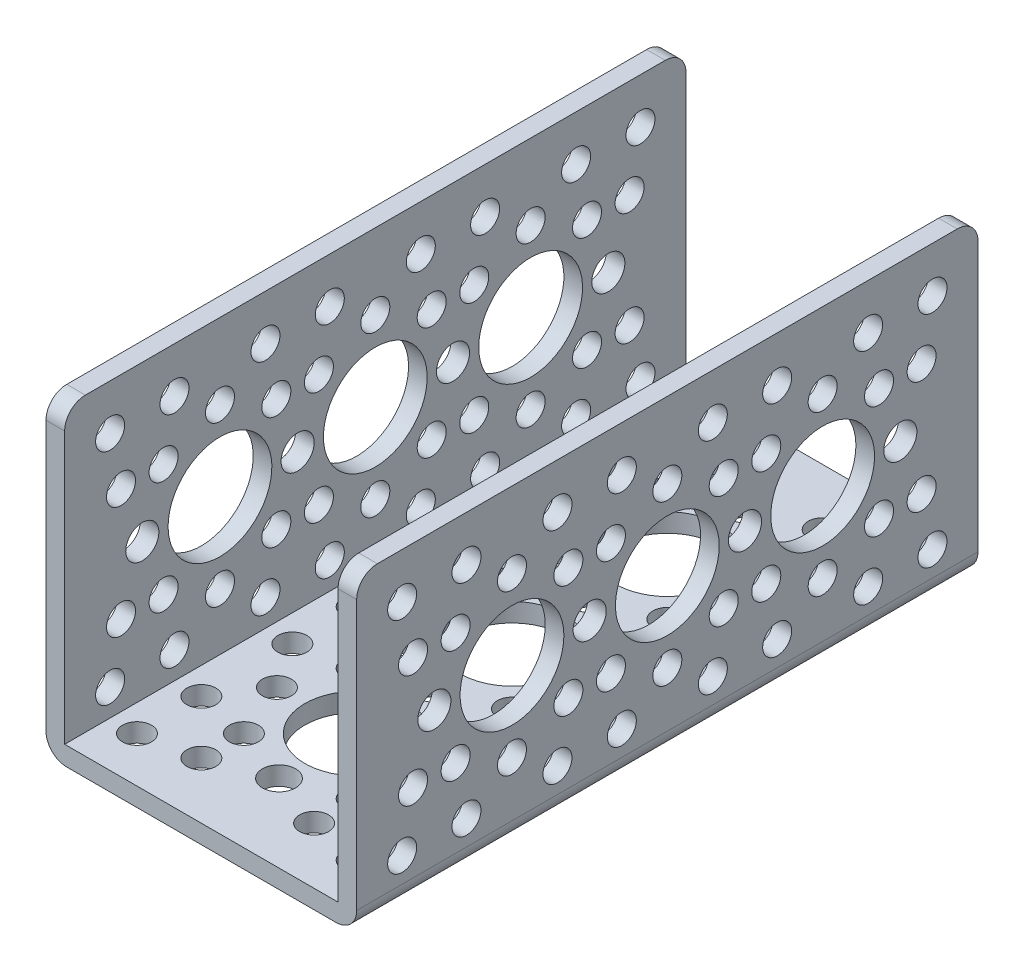
SolidWorks part; units mm, degrees
ref_plane "Front Plane" through (0, 0, 0) normal (0, 0, 1) x (1, 0, 0)
ref_plane "Top Plane" through (0, 0, 0) normal (0, 1, 0) x (1, 0, 0)
ref_plane "Right Plane" through (0, 0, 0) normal (1, 0, 0) x (0, 0, -1)
ref_plane "Plane1" through (0, 0, 0) normal (0, -1, 0) x (1, 0, 0)
sketch "Sketch1" plane through (0, 0, 0) normal (0, -1, 0) x (1, 0, 0)
  line L0 (38.1, 76.2) -> (0, 76.2)
  line L1 (0, 76.2) -> (0, 0)
  line L2 (0, 0) -> (38.1, 0)
  line L3 (38.1, 0) -> (38.1, 76.2)
extrude "Boss-Extrude1" add sketch "Sketch1" against normal blind 38.1
sketch "Sketch2" plane through (0, 0, 76.2) normal (0, 0, 1) x (1, 0, 0)
  line L0 (35.814, 38.1) -> (2.286, 38.1)
  line L1 (2.286, 38.1) -> (2.286, 2.286)
  line L2 (2.286, 2.286) -> (35.814, 2.286)
  line L3 (35.814, 2.286) -> (35.814, 38.1)
extrude "Cut-Extrude1" cut sketch "Sketch2" against normal through all
hole_wizard "Hole1" positions "Sketch4" profile "Sketch3" legacy
sketch "Sketch4" plane through (38.1, 0, 0) normal (1, 0, 0) x (0, 0, -1)
  point P0 (-38.1, 19.05)
  point P1 (-19.05, 19.05)
  point P2 (-57.15, 19.05)
sketch "Sketch3" plane through (38.1, 19.05, 38.1) normal (0, 1, 0) x (0, 0, -1)
  line L0 (0, 0) -> (0, 2.286)
  line L1 (0, 2.286) -> (6.3627, 2.286)
  line L2 (6.3627, 2.286) -> (6.3627, 0)
  line L3 (6.3627, 0) -> (0, 0)
  line L4 (0, 110) -> (0, -10) construction
  dimension "Diameter" = 12.7254
  dimension "Depth" = 2.286
hole_wizard "M3 Clearance Hole1" positions "Sketch6" profile "Sketch5" hole size "M3" standard "ANSI Metric"
sketch "Sketch6" plane through (38.1, 0, 0) normal (1, 0, 0) x (0, 0, -1)
  point P0 (-62.7296, 5.5796)
  point P1 (-69.2852, 12.1352)
  point P2 (-62.7296, 32.5204)
  point P3 (-69.2852, 25.9648)
  point P4 (-13.4704, 5.5796)
  point P5 (-6.9148, 12.1352)
  point P6 (-13.4704, 32.5204)
  point P7 (-6.9148, 25.9648)
  point P8 (-43.6796, 5.5796)
  point P9 (-24.6296, 5.5796)
  point P10 (-43.6796, 32.5204)
  point P11 (-24.6296, 32.5204)
  point P12 (-70.6204, 5.5796)
  point P13 (-70.6204, 32.5204)
  point P14 (-51.5704, 5.5796)
  point P15 (-51.5704, 32.5204)
  point P16 (-50.2352, 12.1352)
  point P17 (-57.15, 9.271)
  point P18 (-64.0648, 12.1352)
  point P19 (-64.0648, 25.9648)
  point P20 (-57.15, 28.829)
  point P21 (-31.1852, 12.1352)
  point P22 (-38.1, 9.271)
  point P23 (-45.0148, 12.1352)
  point P24 (-45.0148, 25.9648)
  point P25 (-38.1, 28.829)
  point P26 (-50.2352, 25.9648)
  point P27 (-31.1852, 25.9648)
  point P28 (-32.5204, 5.5796)
  point P29 (-32.5204, 32.5204)
  point P30 (-5.5796, 5.5796)
  point P31 (-5.5796, 32.5204)
  point P32 (-12.1352, 12.1352)
  point P33 (-19.05, 9.271)
  point P34 (-25.9648, 12.1352)
  point P35 (-25.9648, 25.9648)
  point P36 (-19.05, 28.829)
  point P37 (-12.1352, 25.9648)
sketch "Sketch5" plane through (38.1, 5.5796, 62.7296) normal (0, 1, 0) x (0, 0, -1)
  line L0 (0, 0) -> (0, 2.286)
  line L1 (0, 2.286) -> (1.778, 2.286)
  line L2 (1.778, 2.286) -> (1.778, 0)
  line L5 (1.778, 0) -> (0, 0)
  line L11 (0, -6.35) -> (0, 107.95) construction
  dimension "Thru Hole Dia." = 3.556
  dimension "Thru Hole Depth" = 2.286
hole_wizard "M3.5 Clearance Hole1" positions "Sketch8" profile "Sketch7" hole size "M3.5" standard "ANSI Metric"
sketch "Sketch8" plane through (38.1, 0, 0) normal (1, 0, 0) x (0, 0, -1)
  point P0 (-66.675, 19.05)
  point P1 (-47.625, 19.05)
  point P2 (-28.575, 19.05)
  point P3 (-9.525, 19.05)
sketch "Sketch7" plane through (38.1, 19.05, 66.675) normal (0, 1, 0) x (0, 0, -1)
  line L0 (0, 0) -> (0, 2.286)
  line L1 (0, 2.286) -> (2.032, 2.286)
  line L2 (2.032, 2.286) -> (2.032, 0)
  line L5 (2.032, 0) -> (0, 0)
  line L11 (0, -6.35) -> (0, 107.95) construction
  dimension "Thru Hole Dia." = 4.064
  dimension "Thru Hole Depth" = 2.286
hole_wizard "Hole2" positions "Sketch10" profile "Sketch9" legacy
sketch "Sketch10" plane through (0, 0, 0) normal (0, -1, 0) x (-1, 0, 0)
  point P0 (-19.05, -57.15)
  point P1 (-19.05, -38.1)
  point P2 (-19.05, -19.05)
sketch "Sketch9" plane through (19.05, 0, 57.15) normal (1, 0, 0) x (0, 0, -1)
  line L0 (0, 0) -> (0, 38.1)
  line L1 (0, 38.1) -> (6.3627, 38.1)
  line L2 (6.3627, 38.1) -> (6.3627, 0)
  line L3 (6.3627, 0) -> (0, 0)
  line L4 (0, 110) -> (0, -10) construction
  dimension "Diameter" = 12.7254
  dimension "Depth" = 38.1
hole_wizard "M3.5 Clearance Hole2" positions "Sketch12" profile "Sketch11" hole size "M3.5" standard "ANSI Metric"
sketch "Sketch12" plane through (0, 0, 0) normal (0, -1, 0) x (-1, 0, 0)
  point P0 (-19.05, -66.675)
  point P1 (-19.05, -47.625)
  point P2 (-19.05, -28.575)
  point P3 (-19.05, -9.525)
sketch "Sketch11" plane through (19.05, 0, 66.675) normal (1, 0, 0) x (0, 0, -1)
  line L0 (0, 0) -> (0, 38.1)
  line L1 (0, 38.1) -> (2.032, 38.1)
  line L2 (2.032, 38.1) -> (2.032, 0)
  line L5 (2.032, 0) -> (0, 0)
  line L11 (0, -6.35) -> (0, 107.95) construction
  dimension "Thru Hole Dia." = 4.064
  dimension "Thru Hole Depth" = 38.1
hole_wizard "M3 Clearance Hole2" positions "Sketch14" profile "Sketch13" hole size "M3" standard "ANSI Metric"
sketch "Sketch14" plane through (0, 0, 0) normal (0, -1, 0) x (-1, 0, 0)
  point P0 (-5.5796, -70.6204)
  point P1 (-5.5796, -62.7296)
  point P2 (-12.1352, -69.2852)
  point P3 (-32.5204, -70.6204)
  point P4 (-32.5204, -62.7296)
  point P5 (-25.9648, -69.2852)
  point P6 (-5.5796, -51.5704)
  point P7 (-5.5796, -43.6796)
  point P8 (-32.5204, -51.5704)
  point P9 (-32.5204, -43.6796)
  point P10 (-12.1352, -50.2352)
  point P11 (-9.271, -57.15)
  point P12 (-12.1352, -64.0648)
  point P13 (-25.9648, -64.0648)
  point P14 (-28.829, -57.15)
  point P15 (-25.9648, -50.2352)
  point P16 (-9.271, -38.1)
  point P17 (-12.1352, -45.0148)
  point P18 (-25.9648, -45.0148)
  point P19 (-28.829, -38.1)
  point P20 (-5.5796, -32.5204)
  point P21 (-5.5796, -24.6296)
  point P22 (-12.1352, -31.1852)
  point P23 (-32.5204, -32.5204)
  point P24 (-32.5204, -24.6296)
  point P25 (-25.9648, -31.1852)
  point P26 (-5.5796, -5.5796)
  point P27 (-5.5796, -13.4704)
  point P28 (-12.1352, -6.9148)
  point P29 (-32.5204, -5.5796)
  point P30 (-32.5204, -13.4704)
  point P31 (-25.9648, -6.9148)
  point P32 (-12.1352, -12.1352)
  point P33 (-9.271, -19.05)
  point P34 (-12.1352, -25.9648)
  point P35 (-25.9648, -25.9648)
  point P36 (-28.829, -19.05)
  point P37 (-25.9648, -12.1352)
sketch "Sketch13" plane through (5.5796, 0, 70.6204) normal (1, 0, 0) x (0, 0, -1)
  line L0 (0, 0) -> (0, 38.1)
  line L1 (0, 38.1) -> (1.778, 38.1)
  line L2 (1.778, 38.1) -> (1.778, 0)
  line L5 (1.778, 0) -> (0, 0)
  line L11 (0, -6.35) -> (0, 107.95) construction
  dimension "Thru Hole Dia." = 3.556
  dimension "Thru Hole Depth" = 38.1
hole_wizard "Hole3" positions "Sketch16" profile "Sketch15" legacy
sketch "Sketch16" plane through (0, 0, 0) normal (-1, 0, 0) x (0, 0, 1)
  point P0 (38.1, 19.05)
  point P1 (19.05, 19.05)
  point P2 (57.15, 19.05)
sketch "Sketch15" plane through (0, 19.05, 38.1) normal (0, 1, 0) x (0, 0, 1)
  line L0 (0, 0) -> (0, 38.1)
  line L1 (0, 38.1) -> (6.3627, 38.1)
  line L2 (6.3627, 38.1) -> (6.3627, 0)
  line L3 (6.3627, 0) -> (0, 0)
  line L4 (0, 110) -> (0, -10) construction
  dimension "Diameter" = 12.7254
  dimension "Depth" = 38.1
hole_wizard "M3 Clearance Hole3" positions "Sketch18" profile "Sketch17" hole size "M3" standard "ANSI Metric"
sketch "Sketch18" plane through (0, 0, 0) normal (-1, 0, 0) x (0, 0, 1)
  point P0 (62.7296, 5.5796)
  point P1 (69.2852, 12.1352)
  point P2 (62.7296, 32.5204)
  point P3 (69.2852, 25.9648)
  point P4 (13.4704, 5.5796)
  point P5 (6.9148, 12.1352)
  point P6 (13.4704, 32.5204)
  point P7 (6.9148, 25.9648)
  point P8 (43.6796, 5.5796)
  point P9 (24.6296, 5.5796)
  point P10 (43.6796, 32.5204)
  point P11 (24.6296, 32.5204)
  point P12 (70.6204, 5.5796)
  point P13 (70.6204, 32.5204)
  point P14 (51.5704, 5.5796)
  point P15 (51.5704, 32.5204)
  point P16 (50.2352, 12.1352)
  point P17 (57.15, 9.271)
  point P18 (64.0648, 12.1352)
  point P19 (64.0648, 25.9648)
  point P20 (57.15, 28.829)
  point P21 (31.1852, 12.1352)
  point P22 (38.1, 9.271)
  point P23 (45.0148, 12.1352)
  point P24 (45.0148, 25.9648)
  point P25 (38.1, 28.829)
  point P26 (50.2352, 25.9648)
  point P27 (31.1852, 25.9648)
  point P28 (32.5204, 5.5796)
  point P29 (32.5204, 32.5204)
  point P30 (5.5796, 5.5796)
  point P31 (5.5796, 32.5204)
  point P32 (12.1352, 12.1352)
  point P33 (19.05, 9.271)
  point P34 (25.9648, 12.1352)
  point P35 (25.9648, 25.9648)
  point P36 (19.05, 28.829)
  point P37 (12.1352, 25.9648)
sketch "Sketch17" plane through (0, 5.5796, 62.7296) normal (0, 1, 0) x (0, 0, 1)
  line L0 (0, 0) -> (0, 38.1)
  line L1 (0, 38.1) -> (1.778, 38.1)
  line L2 (1.778, 38.1) -> (1.778, 0)
  line L5 (1.778, 0) -> (0, 0)
  line L11 (0, -6.35) -> (0, 107.95) construction
  dimension "Thru Hole Dia." = 3.556
  dimension "Thru Hole Depth" = 38.1
hole_wizard "M3.5 Clearance Hole3" positions "Sketch20" profile "Sketch19" hole size "M3.5" standard "ANSI Metric"
sketch "Sketch20" plane through (0, 0, 0) normal (-1, 0, 0) x (0, 0, 1)
  point P0 (66.675, 19.05)
  point P1 (47.625, 19.05)
  point P2 (28.575, 19.05)
  point P3 (9.525, 19.05)
sketch "Sketch19" plane through (0, 19.05, 66.675) normal (0, 1, 0) x (0, 0, 1)
  line L0 (0, 0) -> (0, 38.1)
  line L1 (0, 38.1) -> (2.032, 38.1)
  line L2 (2.032, 38.1) -> (2.032, 0)
  line L5 (2.032, 0) -> (0, 0)
  line L11 (0, -6.35) -> (0, 107.95) construction
  dimension "Thru Hole Dia." = 4.064
  dimension "Thru Hole Depth" = 38.1
fillet "Fillet1" radius 2.54 6 edges at (1.143, 38.1, 76.2) (36.957, 38.1, 76.2) (36.957, 38.1, 0) (38.1, 0, 38.1) (1.143, 38.1, 0) (0, 0, 38.1)
